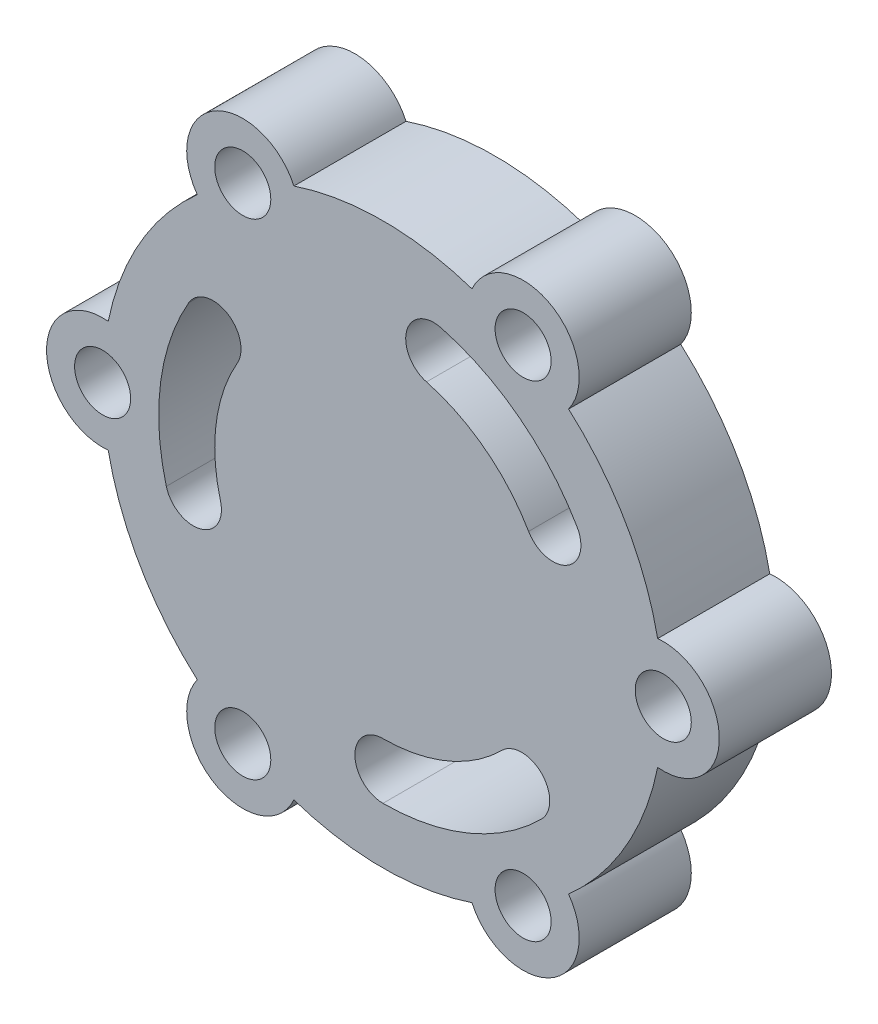
SolidWorks part; units mm, degrees
ref_plane "Front Plane" through (0, 0, 0) normal (0, 0, 1) x (1, 0, 0)
ref_plane "Top Plane" through (0, 0, 0) normal (0, 1, 0) x (1, 0, 0)
ref_plane "Right Plane" through (0, 0, 0) normal (1, 0, 0) x (0, 0, -1)
sketch "Sketch2" plane through (0, 0, 0) normal (0, 0, 1) x (1, 0, 0)
  line L0 (0, 0) -> (8.4784, 0) construction
  line L1 (0, 0) -> (0, 9.9499) construction
  line L2 (0, 0) -> (60.6218, 35) construction
  circle A0 centre (0, 0) radius 35 construction
  arc A1 (-49, -9.9499) -> (-33.1168, -37.4603) centre (0, 0) ccw
  arc A2 (-49, -9.9499) -> (-33.1168, -37.4603) centre (0, 0) ccw construction
  arc A3 (-49, 9.9499) -> (-49, -9.9499) centre (-50, 0) ccw
  circle A4 centre (-50, 0) radius 5
  arc A5 (9.0587, 33.8074) -> (30.3109, 17.5) centre (0, 0) cw construction
  arc A10 (34.641, 20) -> (10.3528, 38.637) centre (0, 0) ccw
  arc A15 (25.9808, 15) -> (7.7646, 28.9778) centre (0, 0) ccw
  arc A20 (-33.1168, 37.4603) -> (-33.1168, -37.4603) centre (0, 0) ccw construction
  arc A21 (-15.8832, 47.4102) -> (-33.1168, 37.4603) centre (-25, 43.3013) ccw
  circle A22 centre (-25, 43.3013) radius 5
  arc A23 (33.1168, 37.4603) -> (15.8832, 47.4102) centre (25, 43.3013) ccw
  circle A24 centre (25, 43.3013) radius 5
  arc A25 (49, -9.9499) -> (49, 9.9499) centre (50, 0) ccw
  circle A26 centre (50, 0) radius 5
  arc A27 (15.8832, -47.4102) -> (33.1168, -37.4603) centre (25, -43.3013) ccw
  circle A28 centre (25, -43.3013) radius 5
  arc A29 (-33.1168, -37.4603) -> (-15.8832, -47.4102) centre (-25, -43.3013) ccw
  circle A30 centre (-25, -43.3013) radius 5
  arc A31 (-33.1168, 37.4603) -> (-49, 9.9499) centre (0, 0) ccw
  arc A32 (-33.1168, 37.4603) -> (-49, 9.9499) centre (0, 0) ccw construction
  arc A33 (15.8832, 47.4102) -> (-15.8832, 47.4102) centre (0, 0) ccw
  arc A34 (15.8832, 47.4102) -> (-15.8832, 47.4102) centre (0, 0) ccw construction
  arc A35 (15.8832, 47.4102) -> (-15.8832, 47.4102) centre (0, 0) ccw construction
  arc A36 (33.1168, -37.4603) -> (49, -9.9499) centre (0, 0) ccw
  arc A37 (33.1168, -37.4603) -> (49, -9.9499) centre (0, 0) ccw construction
  arc A38 (33.1168, -37.4603) -> (49, -9.9499) centre (0, 0) ccw construction
  arc A39 (49, 9.9499) -> (33.1168, 37.4603) centre (0, 0) ccw
  arc A40 (49, 9.9499) -> (33.1168, 37.4603) centre (0, 0) ccw construction
  arc A41 (49, 9.9499) -> (33.1168, 37.4603) centre (0, 0) ccw construction
  arc A42 (-15.8832, -47.4102) -> (15.8832, -47.4102) centre (0, 0) ccw
  arc A43 (-15.8832, -47.4102) -> (15.8832, -47.4102) centre (0, 0) ccw construction
  arc A44 (-15.8832, -47.4102) -> (15.8832, -47.4102) centre (0, 0) ccw construction
  arc A45 (24.7487, -24.7487) -> (0, -35) centre (0, 0) cw construction
  arc A46 (0, -40) -> (28.2843, -28.2843) centre (0, 0) ccw
  arc A47 (0, -30) -> (21.2132, -21.2132) centre (0, 0) ccw
  arc A48 (0, -30) -> (0, -40) centre (0, -35) ccw
  arc A49 (28.2843, -28.2843) -> (21.2132, -21.2132) centre (24.7487, -24.7487) ccw
  arc A50 (25.9808, 15) -> (34.641, 20) centre (30.3109, 17.5) ccw
  arc A51 (10.3528, 38.637) -> (7.7646, 28.9778) centre (9.0587, 33.8074) ccw
  arc A52 (-33.8074, -9.0587) -> (-30.3109, 17.5) centre (0, 0) cw construction
  arc A53 (-34.641, 20) -> (-38.637, -10.3528) centre (0, 0) ccw
  arc A54 (-25.9808, 15) -> (-28.9778, -7.7646) centre (0, 0) ccw
  arc A55 (-25.9808, 15) -> (-34.641, 20) centre (-30.3109, 17.5) ccw
  arc A56 (-38.637, -10.3528) -> (-28.9778, -7.7646) centre (-33.8074, -9.0587) ccw
  point P10 (21.3067, 27.7674)
  point P26 (13.3939, -32.3358)
  point P53 (-34.8654, 3.0668)
  point P54 (-34.7006, 4.5684)
  dimension "D1" = 70
  dimension "D2" = 100
  dimension "D3" = 20
  dimension "D4" = 10
  dimension "D5" = 10
  dimension "D9" = 3
  dimension "D6" = 45
  dimension "D7" = 30
  dimension "D8" = 6
extrude "Boss-Extrude2" add sketch "Sketch2" along normal blind 20
